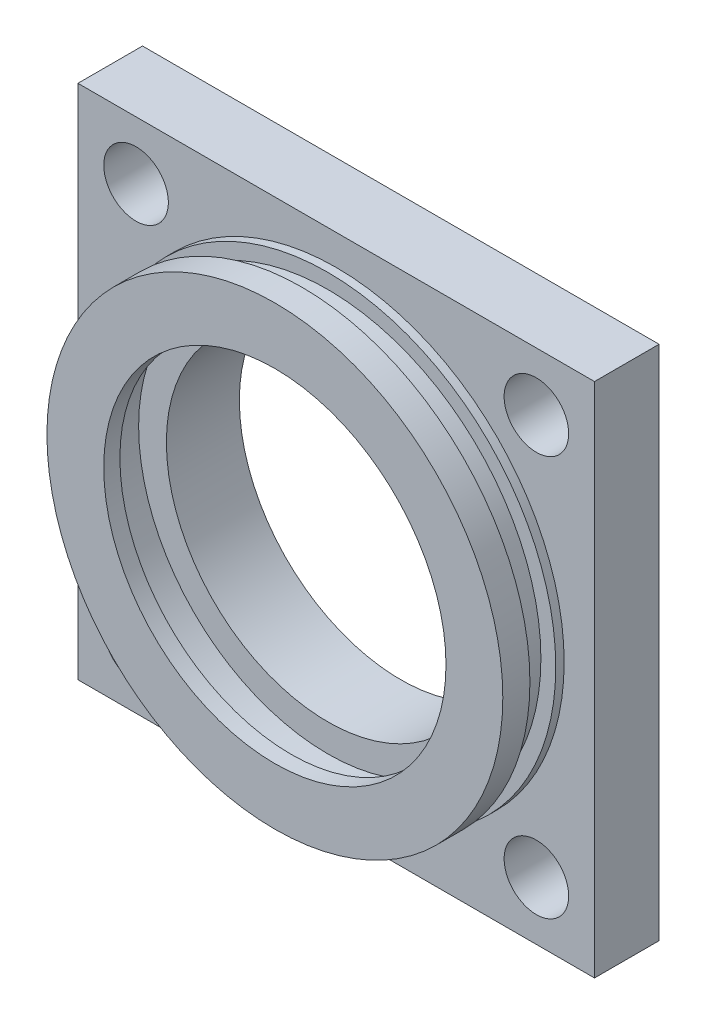
SolidWorks part; units mm, degrees
ref_plane "Front Plane" through (0, 0, 0) normal (0, 0, 1) x (1, 0, 0)
ref_plane "Top Plane" through (0, 0, 0) normal (0, 1, 0) x (1, 0, 0)
ref_plane "Right Plane" through (0, 0, 0) normal (1, 0, 0) x (0, 0, -1)
sketch "Sketch2" plane through (0, 0, 0) normal (0, 0, 1) x (1, 0, 0)
  line L0 (40, 0) -> (-40, 0)
  line L1 (-40, 0) -> (-40, 80)
  line L2 (-40, 80) -> (40, 80)
  line L3 (40, 80) -> (40, 0)
  point P4 (0, 0)
  dimension "D1" = 80
  dimension "D2" = 80
extrude "Boss-Extrude1" add sketch "Sketch2" along normal blind 10
sketch "Sketch3" plane through (0, 0, 10) normal (0, 0, 1) x (1, 0, 0)
  line L0 (-40, 80) -> (40, 0) construction
  line L1 (40, 0) -> (-40, 0) construction
  line L2 (-40, 0) -> (40, 80) construction
  circle A0 centre (0, 40) radius 35.3
  dimension "D1" = 70.6
extrude "Boss-Extrude2" add sketch "Sketch3" along normal blind 9.5
ref_plane "Plane1" through (0, 0, 11.3) normal (0, 0, 1) x (1, 0, 0)
sketch "Sketch5" plane through (0, 0, 11.3) normal (0, 0, 1) x (1, 0, 0)
  circle A0 centre (0, 40) radius 29.3
  dimension "D1" = 58.6
extrude "Cut-Extrude1" cut sketch "Sketch5" along normal blind 5.3
sketch "Sketch6" plane through (0, 0, 11.3) normal (0, 0, 1) x (1, 0, 0)
  circle A0 centre (0, 40) radius 33
  circle A1 centre (0, 40) radius 37.5
  dimension "D1" = 66
  dimension "D2" = 75
extrude "Cut-Extrude4" cut sketch "Sketch6" along normal blind 4
ref_plane "Plane2" through (0, 0, 19.5) normal (0, 0, 1) x (1, 0, 0)
sketch "Sketch8" plane through (0, 0, 19.5) normal (0, 0, 1) x (1, 0, 0)
  circle A0 centre (0, 40) radius 26.5
  dimension "D1" = 53
extrude "Cut-Extrude10" cut sketch "Sketch8" against normal blind 2.5
ref_plane "Plane3" through (0, 0, 17) normal (0, 0, 1) x (1, 0, 0)
sketch "Sketch9" plane through (0, 0, 17) normal (0, 0, 1) x (1, 0, 0)
  circle A0 centre (0, 40) radius 29.3
  dimension "D1" = 58.6
extrude "Cut-Extrude11" cut sketch "Sketch9" against normal blind 5.3
sketch "Sketch10" plane through (0, 0, 0) normal (0, 0, -1) x (-1, 0, 0)
  line L0 (-40, 80) -> (40, 0) construction
  line L1 (40, 0) -> (-40, 0) construction
  line L2 (-40, 0) -> (40, 80) construction
  circle A0 centre (0, 40) radius 25
  dimension "D1" = 50
extrude "Cut-Extrude12" cut sketch "Sketch10" against normal blind 11.3
sketch "Sketch11" plane through (0, 0, 0) normal (0, 0, 1) x (1, 0, 0)
  circle A0 centre (-31, 71) radius 5
  circle A1 centre (31, 71) radius 5
  circle A2 centre (31, 9) radius 5
  circle A3 centre (-31, 9) radius 5
  dimension "D3" = 10
  dimension "D4" = 2
  dimension "D5" = 2
extrude "Cut-Extrude13" cut sketch "Sketch11" against normal blind 36.3 and the other way blind 64
